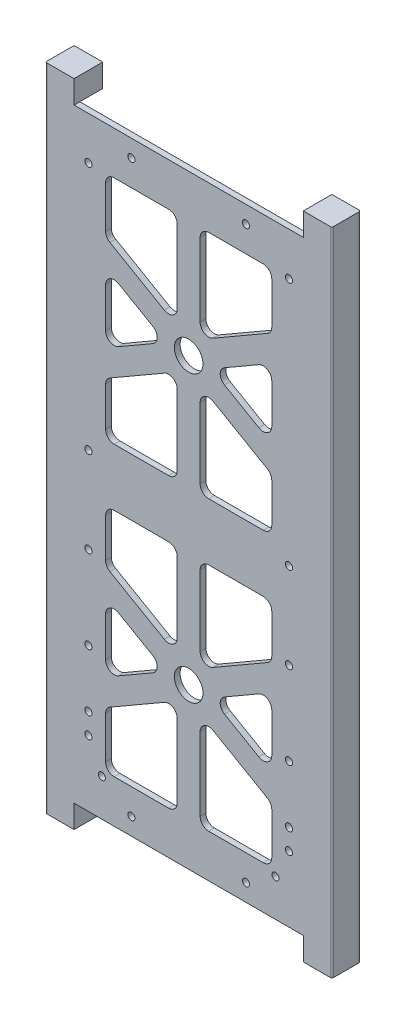
SolidWorks part; units mm, degrees
material "6061-T6 (SS)"
ref_plane "Front Plane" through (0, 0, 0) normal (0, 0, 1) x (1, 0, 0)
ref_plane "Top Plane" through (0, 0, 0) normal (0, 1, 0) x (1, 0, 0)
ref_plane "Right Plane" through (0, 0, 0) normal (1, 0, 0) x (0, 0, -1)
sketch "Sketch1" plane through (0, 0, 0) normal (0, 0, 1) x (1, 0, 0)
  line L1 (0, 0) -> (88, 0)
  line L2 (0, 0) -> (0, 211)
  line L3 (0, 211) -> (88, 211)
  line L4 (88, 0) -> (88, 211)
  dimension "D1" = 88
  dimension "D2" = 211
extrude "Boss-Extrude1" add sketch "Sketch1" along normal blind 2
sketch "Sketch2" plane through (0, 0, 2) normal (0, 0, 1) x (1, 0, 0)
  line L0 (0, 105.5) -> (88, 105.5) construction
  line L1 (0, 211) -> (0, 0) construction
  line L2 (88, 0) -> (88, 211) construction
  line L3 (44, 211) -> (44, 0) construction
  line L4 (88, 211) -> (0, 211) construction
  line L5 (0, 0) -> (88, 0) construction
  line L6 (0, 155.25) -> (88, 155.25) construction
  line L7 (0, 55.75) -> (88, 55.75) construction
  dimension "D1" = 55.75
  dimension "D2" = 55.75
sketch "Sketch3" plane through (0, 0, 2) normal (0, 0, 1) x (1, 0, 0)
  line L0 (0, 155.25) -> (88, 155.25) construction
  line L2 (0, 211) -> (0, 0) construction
  line L3 (15, 196) -> (73, 196)
  line L4 (15, 196) -> (15, 115.5)
  line L5 (15, 115.5) -> (73, 115.5)
  line L6 (73, 196) -> (73, 115.5)
  line L7 (88, 211) -> (0, 211) construction
  line L8 (88, 0) -> (88, 211) construction
  line L9 (0, 105.5) -> (88, 105.5) construction
  line L10 (40, 196) -> (40, 115.5)
  line L11 (48, 196) -> (48, 115.5)
  line L12 (44, 211) -> (44, 0) construction
  line L13 (73, 171.9932) -> (15, 138.5068) construction
  line L14 (15, 171.9932) -> (73, 138.5068) construction
  line L15 (73, 176.612) -> (15, 143.1256)
  line L16 (73, 167.3744) -> (15, 133.888)
  line L17 (15, 176.612) -> (73, 143.1256)
  line L18 (15, 167.3744) -> (73, 133.888)
  circle A0 centre (44, 155.25) radius 5
  dimension "D1" = 10
  dimension "D3" = 15
  dimension "D4" = 15
  dimension "D5" = 15
  dimension "D6" = 10
  dimension "D7" = 8
  dimension "D8" = 4
  dimension "D9" = 30
  dimension "D10" = 30
  dimension "D11" = 8
  dimension "D12" = 4
  dimension "D13" = 4
  dimension "D14" = 8
ref_plane "Plane1" through (0, 105.5, 0) normal (0, -1, 0) x (1, 0, 0)
extrude "Cut-Extrude2" cut sketch "Sketch3" against normal blind 2 contours L18 L11 L5 L6 | L10 L16 L4 L5 | L18 L4 L15 | L16 L17 L6 | L15 L6 L3 L11 | L4 L17 L10 L3
sketch "Sketch4" plane through (0, 0, 2) normal (0, 0, 1) x (1, 0, 0)
  line L0 (0, 155.25) -> (88, 155.25) construction
  circle A0 centre (44, 155.25) radius 5
  dimension "D1" = 10
extrude "Cut-Extrude3" cut sketch "Sketch4" against normal through all
mirror "Mirror2" about plane through (0, 105.5, 0) normal (0, -1, 0) of "Cut-Extrude3", "Cut-Extrude2"
fillet "Fillet2" radius 3 44 edges at (73, 67.8744, 1) (73, 43.6256, 1) (52, 55.75, 1) (40, 48.8218, 1) (40, 15, 1) (15, 15, 1) (15, 34.388, 1) (15, 143.1256, 1) (15, 167.3744, 1) (36, 155.25, 1) (15, 115.5, 1) (15, 133.888, 1) (40, 148.3218, 1) (40, 115.5, 1) (48, 196, 1) (73, 196, 1) (48, 162.1782, 1) (73, 115.5, 1) (48, 115.5, 1) (48, 148.3218, 1) (73, 133.888, 1) (15, 196, 1) (40, 196, 1) (40, 162.1782, 1) (15, 176.612, 1) (73, 167.3744, 1) (73, 143.1256, 1) (52, 155.25, 1) (48, 62.6782, 1) (48, 95.5, 1) (73, 95.5, 1) (73, 77.112, 1) (73, 34.388, 1) (73, 15, 1) (48, 15, 1) (48, 48.8218, 1) (40, 62.6782, 1) (15, 77.112, 1) (15, 95.5, 1) (40, 95.5, 1) (15, 43.6256, 1) (15, 67.8744, 1) (36, 55.75, 1) (73, 176.612, 1)
sketch "Sketch5" plane through (0, 0, 2) normal (0, 0, 1) x (1, 0, 0)
  line L0 (88, 0) -> (88, 211) construction
  line L1 (0, 211) -> (0, 0) construction
  line L4 (0, 5.5) -> (88, 5.5) construction
  line L5 (0, 0) -> (88, 0) construction
  line L6 (0, 205.5) -> (88, 205.5) construction
  circle A1 centre (64, 205.5) radius 1.5
  circle A3 centre (64, 5.5) radius 1.5
  circle A4 centre (24, 5.5) radius 1.5
  circle A5 centre (24, 205.5) radius 1.5
  dimension "D5" = 3
  dimension "D2" = 40
  dimension "D3" = 24
  dimension "D1" = 200
  dimension "D4" = 5.5
  dimension "D6" = 3
  dimension "D7" = 40
  dimension "D8" = 24
  dimension "D9" = 3
  dimension "D10" = 24
  dimension "D11" = 24
  dimension "D12" = 3
sketch "Sketch7" plane through (0, 0, 2) normal (0, 0, 1) x (1, 0, 0)
  line L0 (0, 105.5) -> (151.3859, 105.5) construction
  line L5 (0, 211) -> (0, 0) construction
  line L7 (44, 211) -> (44, 0) construction
  line L8 (88, 211) -> (0, 211) construction
  line L9 (0, 0) -> (88, 0) construction
  line L17 (94, 219) -> (84, 219)
  line L53 (88, 0) -> (88, 211)
  line L54 (84, 219) -> (84, 211)
  line L55 (84, 0) -> (88, 0)
  line L56 (94, 0) -> (94, 211)
  line L57 (94, -8) -> (94, 219)
  line L58 (88, 211) -> (0, 211) construction
  line L59 (84, 211) -> (88, 211)
  line L60 (84, -8) -> (84, 0)
  line L61 (94, -8) -> (84, -8)
  line L62 (-6, -8) -> (4, -8)
  line L63 (4, -8) -> (4, 0)
  line L64 (4, 0) -> (0, 0)
  line L65 (0, 0) -> (0, 211)
  line L66 (4, 211) -> (0, 211)
  line L67 (4, 219) -> (4, 211)
  line L68 (-6, 219) -> (4, 219)
  line L69 (-6, -8) -> (-6, 219)
  dimension "D1" = 6
extrude "Boss-Extrude2" add sketch "Sketch7" against normal blind 10
sketch "Sketch53" plane through (0, 0, -8) normal (0, 0, -1) x (-1, 0, 0)
  line L0 (-84, 0) -> (-84, 211)
  line L1 (-84, 211) -> (-90, 211)
  line L2 (-92, 209) -> (-92, 2)
  line L4 (-44, 0) -> (-44, 211)
  line L5 (-4, 0) -> (-84, 0) construction
  line L6 (-84, 211) -> (-4, 211) construction
  line L8 (-90, 0) -> (-84, 0)
  line L9 (4, 209) -> (4, 2)
  line L10 (-4, 211) -> (2, 211)
  line L11 (-4, 0) -> (-4, 211)
  line L12 (2, 0) -> (-4, 0)
  arc A0 (-92, 209) -> (-90, 211) centre (-90, 209) cw
  arc A1 (-90, 0) -> (-92, 2) centre (-90, 2) cw
  arc A2 (4, 209) -> (2, 211) centre (2, 209) ccw
  arc A3 (2, 0) -> (4, 2) centre (2, 2) ccw
  line M9 (-88, 0) -> (-88, 211)
  dimension "D1" = 2
  dimension "D2" = 2
extrude "Cut-Extrude5" cut sketch "Sketch53" against normal blind 8 contours A1 L8 L1 A0 L2 M9 | L12 A3 L9 A2 L10 L11
hole_wizard "M3x0.5 Tapped Hole1" positions "Sketch55" profile "Sketch56" tap size "M3x0.5" standard "ANSI Metric"
sketch "Sketch55" plane through (0, 0, 2) normal (0, 0, 1) x (1, 0, 0)
  line L0 (-6, 219) -> (-6, -8) construction
  line L1 (84, 211) -> (4, 211) construction
  line L3 (44, 211) -> (44, 0) construction
  line L4 (4, 0) -> (84, 0) construction
  line L5 (4, 0) -> (84, 0) construction
  line L6 (9, 30.2) -> (9, 211) construction
  point P4 (9, 109.2)
  point P6 (9, 79.2)
  point P8 (9, 50.2)
  point P10 (9, 30.2)
  point P25 (13.7, 13)
  point P40 (24, 205)
  point P42 (24, 6)
  point P44 (9, 23)
  point P47 (9, 196)
  point P48 (0, 0)
  point P49 (0, 0)
  dimension "D2" = 35
  dimension "D4" = 101.8
  dimension "D5" = 20
  dimension "D6" = 29
  dimension "D7" = 30
  dimension "D8" = 15
  dimension "D9" = 23
  dimension "D10" = 20
  dimension "D11" = 6
  dimension "D12" = 19.7
  dimension "D13" = 13
  dimension "D15" = 6
sketch "Sketch56" plane through (9, 109.2, 2) normal (1, 0, 0) x (0, -1, 0)
  line L0 (0, 0) -> (0, 10.7511)
  line L1 (0, 10.7511) -> (1.25, 10)
  line L2 (1.25, 10) -> (1.25, 0)
  line L5 (1.25, 0) -> (0, 0)
  line L10 (0, 10.7511) -> (-1.25, 10) construction
  line L11 (0, -6.35) -> (0, 107.95) construction
  dimension "Tap Drill Dia." = 2.5
  dimension "Tap Drill Depth" = 10
  dimension "Drill Angle" = 118
ref_plane "Plane2" through (44, 0, 0) normal (-1, 0, 0) x (0, 0, 1)
mirror "Mirror3" about plane through (44, 0, 0) normal (-1, 0, 0) of "M3x0.5 Tapped Hole1"
ref_plane "Plane3" through (44, 0, 0) normal (1, 0, 0) x (0, 0, -1)
sketch "Sketch58" plane through (0, 0, 0) normal (0, 0, -1) x (-1, 0, 0)
  line L0 (-13.7, 13) -> (6, 13) construction
  line L1 (6, 219) -> (6, -8) construction
  line L2 (-14.95, 13) -> (-12.45, 13) construction
  line L3 (-13.7, 11.75) -> (-13.7, 14.25) construction
  circle A0 centre (-0.7, 13) radius 1.665
  circle A1 centre (-13.7, 13) radius 1.25 construction
  point P9 (-13.7, 13)
  dimension "D1" = 3.33
  dimension "D2" = 13
extrude "Cut-Extrude9" cut sketch "Sketch58" against normal blind 1.8 contours A0
mirror "Mirror4" about plane through (44, 0, 0) normal (1, 0, 0) of "Cut-Extrude9"
sketch "Sketch59" plane through (0, -8, 0) normal (0, -1, 0) x (-1, 0, 0)
  line L0 (-94, 8) -> (-94, -2) construction
  line L1 (6, 8) -> (6, -2) construction
  line L2 (-84, 8) -> (-94, 8) construction
  circle A0 centre (-89, 2.4) radius 2
  circle A1 centre (1, 2.4) radius 2
  dimension "D1" = 4
  dimension "D2" = 5
  dimension "D3" = 5
  dimension "D4" = 5.6
extrude "Cut-Extrude10" cut sketch "Sketch59" against normal blind 10
fillet "Fillet3" radius 0.5 4 edges at (-6, 105.5, 2) (-6, 105.5, -8) (94, 105.5, -8) (94, 105.5, 2)
